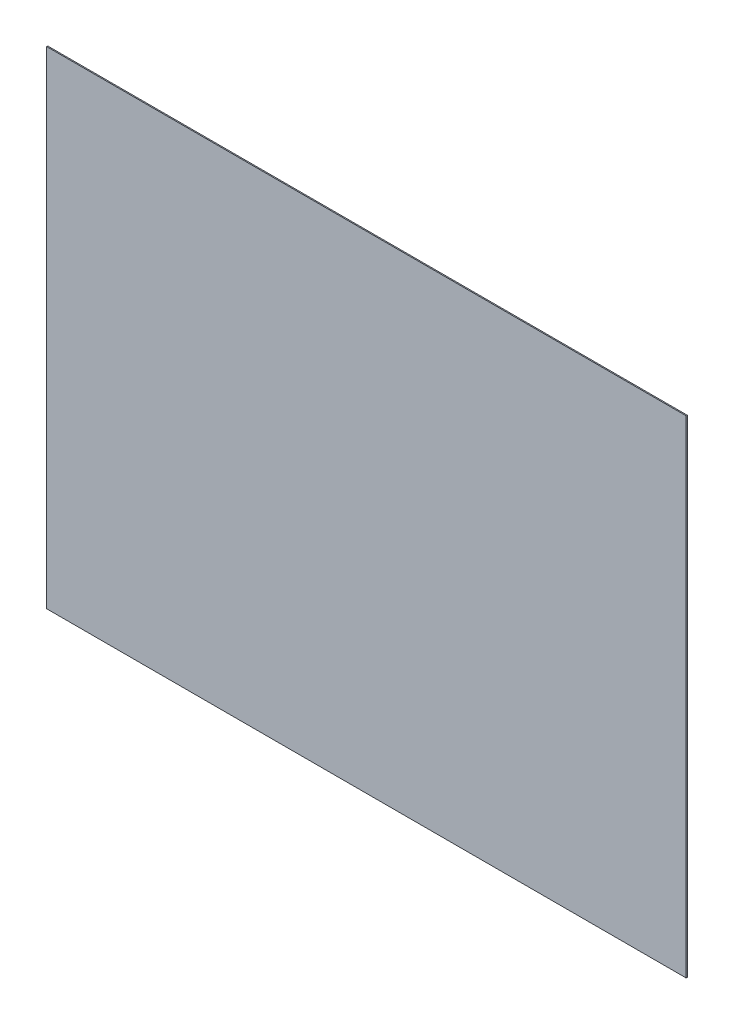
SolidWorks part; units mm, degrees
ref_plane "Front Plane" through (0, 0, 0) normal (0, 0, 1) x (1, 0, 0)
ref_plane "Top Plane" through (0, 0, 0) normal (0, 1, 0) x (1, 0, 0)
ref_plane "Right Plane" through (0, 0, 0) normal (1, 0, 0) x (0, 0, -1)
sketch "Sketch1" plane through (0, 0, 0) normal (0, 0, 1) x (1, 0, 0)
  line L1 (-295.5, 225) -> (295.5, 225)
  line L2 (-295.5, 225) -> (-295.5, -225)
  line L3 (-295.5, -225) -> (295.5, -225)
  line L4 (295.5, 225) -> (295.5, -225)
  line L5 (-295.5, 225) -> (295.5, -225) construction
  line L6 (-295.5, -225) -> (295.5, 225) construction
  point P0 (0, 0)
  dimension "D1" = 591
  dimension "D2" = 450
extrude "Boss-Extrude1" add sketch "Sketch1" along normal blind 1
